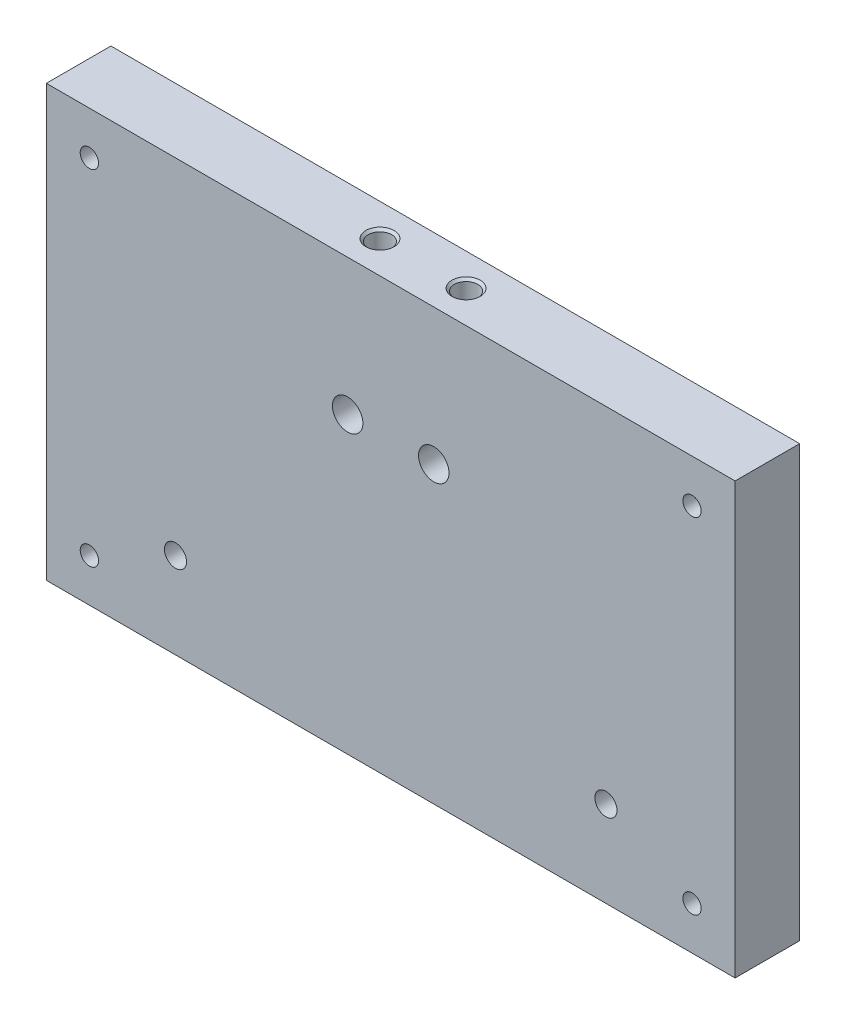
SolidWorks part; units mm, degrees
material "6061-T6 (SS)"
ref_plane "Front Plane" through (0, 0, 0) normal (0, 0, 1) x (1, 0, 0)
ref_plane "Top Plane" through (0, 0, 0) normal (0, 1, 0) x (1, 0, 0)
ref_plane "Right Plane" through (0, 0, 0) normal (1, 0, 0) x (0, 0, -1)
sketch "Sketch1" plane through (0, 0, 0) normal (0, 0, 1) x (1, 0, 0)
  line L1 (0, 0) -> (-101.6, 0)
  line L2 (0, 0) -> (0, 63.5)
  line L3 (0, 63.5) -> (-101.6, 63.5)
  line L4 (-101.6, 0) -> (-101.6, 63.5)
  dimension "D1" = 101.6
  dimension "D2" = 63.5
extrude "Boss-Extrude1" add sketch "Sketch1" along normal blind 9.525
sketch "Sketch5" plane through (0, 63.5, 0) normal (0, 1, 0) x (1, 0, 0)
  line L0 (-101.6, -4.7625) -> (0, -4.7625) construction
  line L1 (-101.6, -9.525) -> (-101.6, 0) construction
  line L2 (0, -9.525) -> (0, 0) construction
  line L3 (-57.15, -4.7625) -> (-44.45, -4.7625)
  point P8 (-50.8, -4.7625)
  dimension "D1" = 12.7
hole_wizard "#8-32 Tapped Hole1" positions "Sketch6" profile "Sketch8" tap size "#8-32" standard "ANSI Inch"
sketch "Sketch6" plane through (0, 63.5, 0) normal (0, 1, 0) x (1, 0, 0)
  point P0 (-44.45, -4.7625)
  point P3 (-57.15, -4.7625)
sketch "Sketch8" plane through (-44.45, 63.5, 4.7625) normal (1, 0, 0) x (0, 0, 1)
  line L0 (0, 0) -> (0, 20.0878)
  line L1 (0, 20.0878) -> (1.7272, 19.05)
  line L2 (1.7272, 19.05) -> (1.7272, 0.3556)
  line L3 (1.7272, 0.3556) -> (2.0828, 0)
  line L5 (2.0828, 0) -> (0, 0)
  line L6 (-1.7272, 0.3556) -> (-2.0828, 0) construction
  line L10 (0, 20.0878) -> (-1.7272, 19.05) construction
  line L11 (0, -6.35) -> (0, 107.95) construction
  dimension "Tap Drill Dia." = 3.4544
  dimension "Tap Drill Depth" = 19.05
  dimension "Near C'Sink Dia." = 4.1656
  dimension "Near C'Sink Angle" = 90
  dimension "Drill Angle" = 118
cosmetic thread "Hole Thread1" parameters "D1"=12.7, "D2"=4.1656
cosmetic thread "Hole Thread2" parameters "D1"=12.7, "D2"=4.1656
hole_wizard "#8 Clearance Hole2" positions "Sketch11" profile "Sketch12" hole size "#8" standard "ANSI Inch"
sketch "Sketch11" plane through (0, 0, 9.525) normal (0, 0, 1) x (1, 0, 0)
  line L0 (-44.45, 43.4122) -> (-42.7228, 44.45) construction
  line L1 (-57.15, 43.4122) -> (-55.4228, 44.45) construction
  line L2 (-44.45, 43.4122) -> (-42.7228, 44.45)
  line L3 (-57.15, 43.4122) -> (-55.4228, 44.45)
  point P1 (-44.45, 43.4122)
  point P3 (-57.15, 43.4122)
sketch "Sketch12" plane through (-44.45, 43.4122, 9.525) normal (1, 0, 0) x (0, -1, 0)
  line L0 (0, 0) -> (0, 26.7507)
  line L1 (0, 26.7507) -> (2.2479, 25.4)
  line L2 (2.2479, 25.4) -> (2.2479, 0)
  line L5 (2.2479, 0) -> (0, 0)
  line L10 (0, 26.7507) -> (-2.2479, 25.4) construction
  line L11 (0, -6.35) -> (0, 107.95) construction
  dimension "Hole Dia." = 4.4958
  dimension "Hole Depth" = 25.4
  dimension "Drill Angle" = 118
sketch "Sketch13" plane through (0, 0, 9.525) normal (0, 0, 1) x (1, 0, 0)
  line L8 (-6.35, 6.35) -> (-6.35, 57.15)
  line L9 (-6.35, 57.15) -> (-95.25, 57.15)
  line L10 (-95.25, 57.15) -> (-95.25, 6.35)
  line L11 (-95.25, 6.35) -> (-6.35, 6.35)
  line L12 (-6.35, 6.35) -> (-6.35, 57.15)
  line L13 (-6.35, 57.15) -> (-95.25, 57.15)
  line L14 (-95.25, 57.15) -> (-95.25, 6.35)
  line L15 (-95.25, 6.35) -> (-6.35, 6.35)
  dimension "D1" = 6.35
hole_wizard "#6-32 Tapped Hole1" positions "Sketch14" profile "Sketch16" tap size "#6-32" standard "ANSI Inch" end condition through all
sketch "Sketch14" plane through (0, 0, 9.525) normal (0, 0, 1) x (1, 0, 0)
  point P0 (-95.25, 6.35)
  point P3 (-95.25, 57.15)
  point P6 (-6.35, 6.35)
  point P9 (-6.35, 57.15)
sketch "Sketch16" plane through (-95.25, 6.35, 9.525) normal (1, 0, 0) x (0, -1, 0)
  line L0 (0, 0) -> (0, 9.525)
  line L1 (0, 9.525) -> (1.3525, 9.525)
  line L2 (1.3525, 9.525) -> (1.3525, 0)
  line L5 (1.3525, 0) -> (0, 0)
  line L11 (0, -6.35) -> (0, 107.95) construction
  dimension "Thru Tap Drill Dia." = 2.7051
  dimension "Thru Tap Drill Depth" = 9.525
cosmetic thread "Hole Thread3" parameters "D2"=3.5052
cosmetic thread "Hole Thread4" parameters "D2"=3.5052
cosmetic thread "Hole Thread5" parameters "D2"=3.5052
cosmetic thread "Hole Thread6" parameters "D2"=3.5052
sketch "Sketch17" plane through (0, 0, 9.525) normal (0, 0, 1) x (1, 0, 0)
  line L0 (-82.55, 12.7) -> (-19.05, 12.7)
  line L1 (-82.55, 12.7) -> (-101.6, 12.7)
  line L2 (-101.6, 63.5) -> (-101.6, 0) construction
  line L3 (-19.05, 12.7) -> (0, 12.7)
  line L4 (0, 0) -> (0, 63.5) construction
  line L5 (-101.6, 0) -> (0, 0) construction
  dimension "D1" = 63.5
  dimension "D2" = 12.7
hole_wizard "#4 Clearance Hole1" positions "Sketch18" profile "Sketch20" hole size "#4" standard "ANSI Inch" end condition up to next
sketch "Sketch18" plane through (0, 0, 9.525) normal (0, 0, 1) x (1, 0, 0)
  point P0 (-82.55, 12.7)
  point P3 (-19.05, 12.7)
sketch "Sketch20" plane through (-82.55, 12.7, 9.525) normal (1, 0, 0) x (0, -1, 0)
  line L0 (0, 0) -> (0, 9.525)
  line L1 (0, 9.525) -> (1.6319, 9.525)
  line L2 (1.6319, 9.525) -> (1.6319, 0)
  line L5 (1.6319, 0) -> (0, 0)
  line L11 (0, -6.35) -> (0, 107.95) construction
  dimension "Thru Hole Dia." = 3.2639
  dimension "Thru Hole Depth" = 9.525
